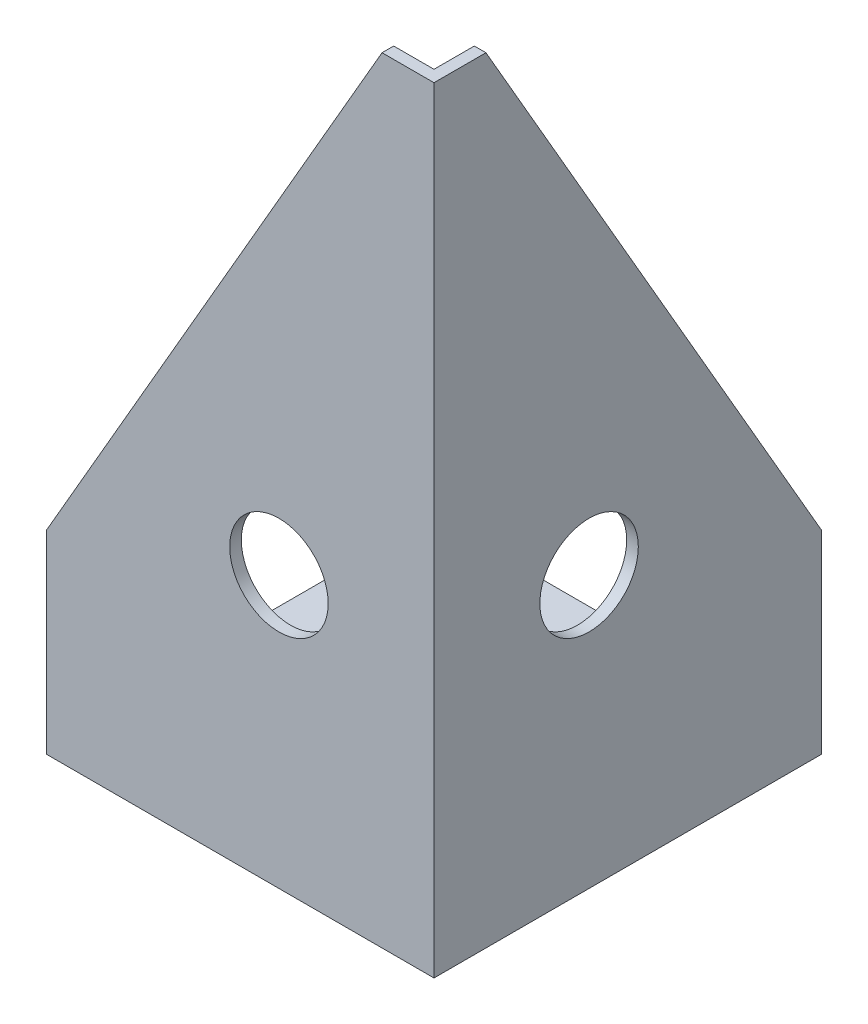
SolidWorks part; units mm, degrees
material "Rostfreier Chromstahl"
ref_plane "Ebene vorne" through (0, 0, 0) normal (0, 0, 1) x (1, 0, 0)
ref_plane "Ebene oben" through (0, 0, 0) normal (0, 1, 0) x (1, 0, 0)
ref_plane "Ebene rechts" through (0, 0, 0) normal (1, 0, 0) x (0, 0, -1)
sketch "Skizze1" plane through (0, 0, 0) normal (0, 1, 0) x (1, 0, 0)
  line L1 (0, 0) -> (100, 0)
  line L2 (0, 0) -> (0, 100)
  line L3 (0, 100) -> (100, 100)
  line L4 (100, 0) -> (100, 100)
  dimension "D1" = 100
extrude "Aufsatz-Linear austragen1" add sketch "Skizze1" along normal blind 200
shell "Wandung1" thickness 3
chamfer "Fase1" distance 150 angle 30 2 edges at (0, 200, -1.5) (98.5, 200, -100)
hole_wizard "Bohrung1" positions "3D-Skizze1" profile "Skizze2" legacy end condition up to next
sketch3d "3D-Skizze1"
  line L0 (100, 200, 0) -> (100, 0, 0) construction
  line L1 (0, 0, 0) -> (100, 0, 0) construction
  line L2 (100, 0, 0) -> (100, 0, -100) construction
  point P0 (100, 70, -40)
  point P2 (60, 70, 0)
  dimension "D1" = 40
  dimension "D2" = 40
  dimension "D3" = 70
  dimension "D4" = 70
sketch "Skizze2" plane through (100, 70, -40) normal (0, 1, 0) x (0, 0, -1)
  line L0 (0, 0) -> (0, 3)
  line L1 (0, 3) -> (12.7, 3)
  line L2 (12.7, 3) -> (12.7, 0)
  line L3 (12.7, 0) -> (0, 0)
  line L4 (0, 110) -> (0, -10) construction
  dimension "Durchmesser" = 25.4
  dimension "Tiefe" = 3
hole_wizard "Durchgangsloch für M101" positions "Skizze4" profile "Skizze3" hole size "M10" standard "DIN" end condition up to next
sketch "Skizze4" plane through (0, 0, 0) normal (0, -1, 0) x (-1, 0, 0)
  line L0 (-100, 100) -> (0, 100) construction
  line L1 (0, 0) -> (-100, 0) construction
  line L2 (-100, 0) -> (-100, 100) construction
  line L3 (0, 100) -> (0, 0) construction
  point P0 (-90, 90)
  point P2 (-90, 10)
  point P4 (-60, 10)
  point P6 (-10, 10)
  dimension "D1" = 10
  dimension "D2" = 10
  dimension "D3" = 10
  dimension "D4" = 10
  dimension "D5" = 40
sketch "Skizze3" plane through (90, 0, -90) normal (1, 0, 0) x (0, 0, -1)
  line L0 (0, 0) -> (0, 3)
  line L1 (0, 3) -> (5.5, 3)
  line L2 (5.5, 3) -> (5.5, 0)
  line L5 (5.5, 0) -> (0, 0)
  line L11 (0, -6.35) -> (0, 107.95) construction
  dimension "Bohrerdurchmesser" = 11
  dimension "Bohrungstiefe" = 3
